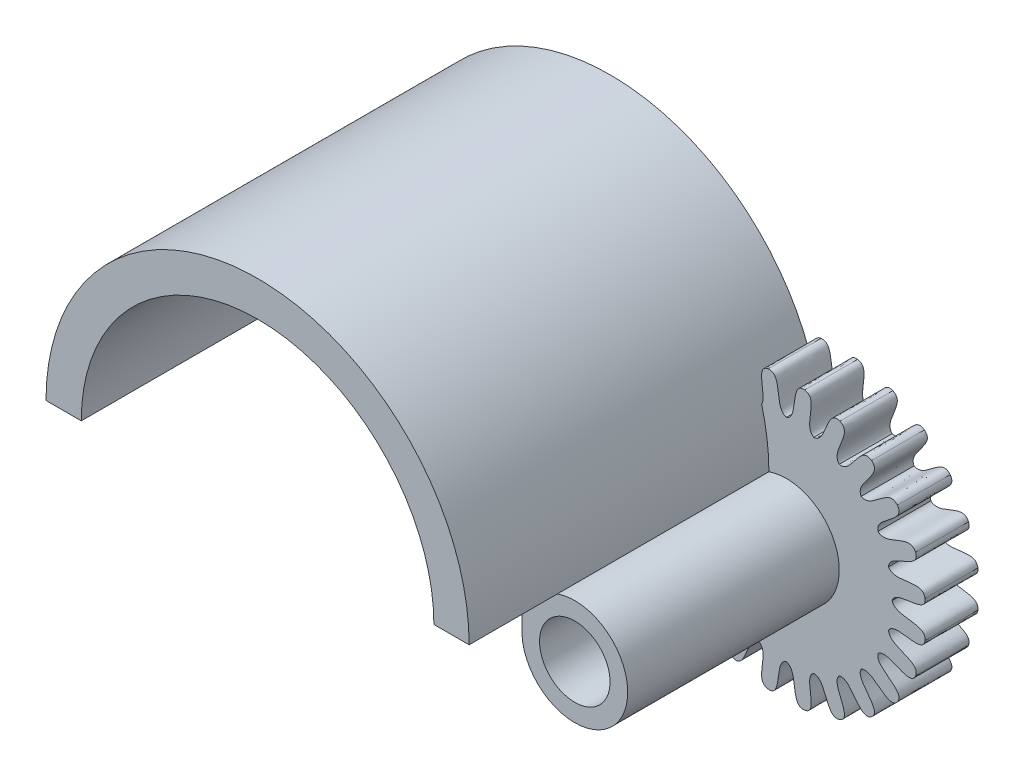
SolidWorks part; units mm, degrees
ref_plane "Front Plane" through (0, 0, 0) normal (0, 0, 1) x (1, 0, 0)
ref_plane "Top Plane" through (0, 0, 0) normal (0, 1, 0) x (1, 0, 0)
ref_plane "Right Plane" through (0, 0, 0) normal (1, 0, 0) x (0, 0, -1)
sketch "Sketch1" plane through (0, 0, 0) normal (0, 0, 1) x (1, 0, 0)
  line L9 (-10, 0) -> (-12, 0)
  line L10 (12, 0) -> (10, 0)
  arc A7 (11.8333, 1.993) -> (-12, 0) centre (0, 0) ccw
  arc A8 (10, 0) -> (-10, 0) centre (0, 0) ccw
  arc A13 (11.94, 1.1985) -> (-12, 0) centre (0, 0) ccw
  arc A15 (11.94, 1.1985) -> (12, 0) centre (0, 0) cw
  dimension "D1" = 24
  dimension "D2" = 20
extrude "Boss-Extrude1" add sketch "Sketch1" along normal blind 20
ref_plane "Plane1" through (-12, 0, 0) normal (-1, 0, 0) x (0, 0, -1)
sketch "Sketch5" plane through (0, 0, 0) normal (0, 0, -1) x (-1, 0, 0)
  line L0 (-10, 0) -> (-10, -2.6091)
  line L1 (-10, 0) -> (-12, 0)
  arc A0 (-12, 0) -> (-10, -2.6091) centre (-12.9918, -2.8313) ccw
  circle A1 centre (-12.9918, -2.8313) radius 2
  dimension "D3" = 4
  dimension "D2" = 3
extrude "Boss-Extrude4" add sketch "Sketch5" against normal blind 15
sketch "Sketch7" plane through (0, 0, 0) normal (0, 0, -1) x (-1, 0, 0)
  line L0 (-12.9918, 5.1687) -> (-12.9918, -2.8313) construction
  line L1 (-12.9918, -2.8313) -> (-15.0623, 4.8961) construction
  line L2 (-15.0623, 4.8961) -> (-12.9918, 5.1687) construction
  line L3 (-14.027, 5.0324) -> (-12.9918, -2.8313)
  circle A0 centre (-12.9918, -2.8313) radius 6
  circle A1 centre (-12.9918, -2.8313) radius 8
  circle A2 centre (-12.9918, -2.8313) radius 2
  spline S0 degree 3 poles (-12.9918, 3.1687) (-13.7122, 3.3663) (-13.1711, 5.1388) (-14.027, 5.0324) knots 0 0 0 0 1 1 1 1
  spline S1 degree 3 poles (-14.5447, 2.9642) (-13.8999, 3.3415) (-14.8813, 4.9137) (-14.027, 5.0324) knots 0 0 0 0 1 1 1 1
  spline S2 degree 3 poles (-11.4388, 2.9642) (-12.0836, 3.3415) (-11.1022, 4.9137) (-11.9565, 5.0324) knots 0 0 0 0 1 1 1 1
  spline S3 degree 3 poles (-12.9918, 3.1687) (-12.2713, 3.3663) (-12.8124, 5.1388) (-11.9565, 5.0324) knots 0 0 0 0 1 1 1 1
  spline S4 degree 3 poles (-9.9918, 2.3648) (-10.5169, 2.8962) (-9.162, 4.1607) (-9.9565, 4.4965) knots 0 0 0 0 1 1 1 1
  spline S5 degree 3 poles (-11.4388, 2.9642) (-10.6918, 2.9686) (-10.7557, 4.8208) (-9.9565, 4.4965) knots 0 0 0 0 1 1 1 1
  spline S6 degree 3 poles (-8.7491, 1.4113) (-9.1188, 2.0605) (-7.4828, 2.9312) (-8.1633, 3.4612) knots 0 0 0 0 1 1 1 1
  spline S7 degree 3 poles (-9.9918, 2.3648) (-9.269, 2.1757) (-8.8514, 3.9813) (-8.1633, 3.4612) knots 0 0 0 0 1 1 1 1
  spline S8 degree 3 poles (-7.7956, 0.1687) (-7.9847, 0.8914) (-6.1791, 1.3091) (-6.6992, 1.9971) knots 0 0 0 0 1 1 1 1
  spline S9 degree 3 poles (-8.7491, 1.4113) (-8.1, 1.0416) (-7.2292, 2.6776) (-6.6992, 1.9971) knots 0 0 0 0 1 1 1 1
  spline S10 degree 3 poles (-7.1962, -1.2784) (-7.1918, -0.5314) (-5.3396, -0.5953) (-5.664, 0.2039) knots 0 0 0 0 1 1 1 1
  spline S11 degree 3 poles (-7.7956, 0.1687) (-7.2643, -0.3565) (-5.9997, 0.9984) (-5.664, 0.2039) knots 0 0 0 0 1 1 1 1
  spline S12 degree 3 poles (-6.9918, -2.8313) (-6.7942, -2.1109) (-5.0216, -2.652) (-5.1281, -1.7961) knots 0 0 0 0 1 1 1 1
  spline S13 degree 3 poles (-7.1962, -1.2784) (-6.8189, -1.9232) (-5.2468, -0.9418) (-5.1281, -1.7961) knots 0 0 0 0 1 1 1 1
  spline S14 degree 3 poles (-7.1962, -4.3842) (-6.8189, -3.7395) (-5.2468, -4.7209) (-5.1281, -3.8666) knots 0 0 0 0 1 1 1 1
  spline S15 degree 3 poles (-6.9918, -2.8313) (-6.7942, -3.5518) (-5.0216, -3.0107) (-5.1281, -3.8666) knots 0 0 0 0 1 1 1 1
  spline S16 degree 3 poles (-7.7956, -5.8313) (-7.2643, -5.3062) (-5.9997, -6.6611) (-5.664, -5.8666) knots 0 0 0 0 1 1 1 1
  spline S17 degree 3 poles (-7.1962, -4.3842) (-7.1918, -5.1313) (-5.3396, -5.0674) (-5.664, -5.8666) knots 0 0 0 0 1 1 1 1
  spline S18 degree 3 poles (-8.7491, -7.074) (-8.1, -6.7042) (-7.2292, -8.3402) (-6.6992, -7.6598) knots 0 0 0 0 1 1 1 1
  spline S19 degree 3 poles (-7.7956, -5.8313) (-7.9847, -6.554) (-6.1791, -6.9717) (-6.6992, -7.6598) knots 0 0 0 0 1 1 1 1
  spline S20 degree 3 poles (-9.9918, -8.0275) (-9.269, -7.8384) (-8.8514, -9.644) (-8.1633, -9.1239) knots 0 0 0 0 1 1 1 1
  spline S21 degree 3 poles (-8.7491, -7.074) (-9.1188, -7.7231) (-7.4828, -8.5939) (-8.1633, -9.1239) knots 0 0 0 0 1 1 1 1
  spline S22 degree 3 poles (-11.4388, -8.6269) (-10.6918, -8.6313) (-10.7557, -10.4835) (-9.9565, -10.1591) knots 0 0 0 0 1 1 1 1
  spline S23 degree 3 poles (-9.9918, -8.0275) (-10.5169, -8.5588) (-9.162, -9.8233) (-9.9565, -10.1591) knots 0 0 0 0 1 1 1 1
  spline S24 degree 3 poles (-12.9918, -8.8313) (-12.2713, -9.0289) (-12.8124, -10.8015) (-11.9565, -10.695) knots 0 0 0 0 1 1 1 1
  spline S25 degree 3 poles (-11.4388, -8.6269) (-12.0836, -9.0042) (-11.1022, -10.5763) (-11.9565, -10.695) knots 0 0 0 0 1 1 1 1
  spline S26 degree 3 poles (-14.5447, -8.6269) (-13.8999, -9.0042) (-14.8813, -10.5763) (-14.027, -10.695) knots 0 0 0 0 1 1 1 1
  spline S27 degree 3 poles (-12.9918, -8.8313) (-13.7122, -9.0289) (-13.1711, -10.8015) (-14.027, -10.695) knots 0 0 0 0 1 1 1 1
  spline S28 degree 3 poles (-15.9918, -8.0275) (-15.4666, -8.5588) (-16.8215, -9.8233) (-16.027, -10.1591) knots 0 0 0 0 1 1 1 1
  spline S29 degree 3 poles (-14.5447, -8.6269) (-15.2917, -8.6313) (-15.2278, -10.4835) (-16.027, -10.1591) knots 0 0 0 0 1 1 1 1
  spline S30 degree 3 poles (-17.2344, -7.074) (-16.8647, -7.7231) (-18.5007, -8.5939) (-17.8202, -9.1239) knots 0 0 0 0 1 1 1 1
  spline S31 degree 3 poles (-15.9918, -8.0275) (-16.7145, -7.8384) (-17.1322, -9.644) (-17.8202, -9.1239) knots 0 0 0 0 1 1 1 1
  spline S32 degree 3 poles (-18.1879, -5.8313) (-17.9988, -6.554) (-19.8044, -6.9717) (-19.2843, -7.6598) knots 0 0 0 0 1 1 1 1
  spline S33 degree 3 poles (-17.2344, -7.074) (-17.8835, -6.7042) (-18.7543, -8.3402) (-19.2843, -7.6598) knots 0 0 0 0 1 1 1 1
  spline S34 degree 3 poles (-18.7873, -4.3842) (-18.7917, -5.1313) (-20.6439, -5.0674) (-20.3196, -5.8666) knots 0 0 0 0 1 1 1 1
  spline S35 degree 3 poles (-18.1879, -5.8313) (-18.7192, -5.3062) (-19.9838, -6.6611) (-20.3196, -5.8666) knots 0 0 0 0 1 1 1 1
  spline S36 degree 3 poles (-18.9918, -2.8313) (-19.1893, -3.5518) (-20.9619, -3.0107) (-20.8555, -3.8666) knots 0 0 0 0 1 1 1 1
  spline S37 degree 3 poles (-18.7873, -4.3842) (-19.1646, -3.7395) (-20.7367, -4.7209) (-20.8555, -3.8666) knots 0 0 0 0 1 1 1 1
  spline S38 degree 3 poles (-18.7873, -1.2784) (-19.1646, -1.9232) (-20.7367, -0.9418) (-20.8555, -1.7961) knots 0 0 0 0 1 1 1 1
  spline S39 degree 3 poles (-18.9918, -2.8313) (-19.1893, -2.1109) (-20.9619, -2.652) (-20.8555, -1.7961) knots 0 0 0 0 1 1 1 1
  spline S40 degree 3 poles (-18.1879, 0.1687) (-18.7192, -0.3565) (-19.9838, 0.9984) (-20.3196, 0.2039) knots 0 0 0 0 1 1 1 1
  spline S41 degree 3 poles (-18.7873, -1.2784) (-18.7917, -0.5314) (-20.6439, -0.5953) (-20.3196, 0.2039) knots 0 0 0 0 1 1 1 1
  spline S42 degree 3 poles (-17.2344, 1.4113) (-17.8835, 1.0416) (-18.7543, 2.6776) (-19.2843, 1.9971) knots 0 0 0 0 1 1 1 1
  spline S43 degree 3 poles (-18.1879, 0.1687) (-17.9988, 0.8914) (-19.8044, 1.3091) (-19.2843, 1.9971) knots 0 0 0 0 1 1 1 1
  spline S44 degree 3 poles (-15.9918, 2.3648) (-16.7145, 2.1757) (-17.1322, 3.9813) (-17.8202, 3.4612) knots 0 0 0 0 1 1 1 1
  spline S45 degree 3 poles (-17.2344, 1.4113) (-16.8647, 2.0605) (-18.5007, 2.9312) (-17.8202, 3.4612) knots 0 0 0 0 1 1 1 1
  spline S46 degree 3 poles (-14.5447, 2.9642) (-15.2917, 2.9686) (-15.2278, 4.8208) (-16.027, 4.4965) knots 0 0 0 0 1 1 1 1
  spline S47 degree 3 poles (-15.9918, 2.3648) (-15.4666, 2.8962) (-16.8215, 4.1607) (-16.027, 4.4965) knots 0 0 0 0 1 1 1 1
  point P129 (-12.9918, -2.8313)
  dimension "D1" = 12
  dimension "D2" = 16
  dimension "D3" = 15
extrude "Boss-Extrude5" add sketch "Sketch7" against normal blind 3
